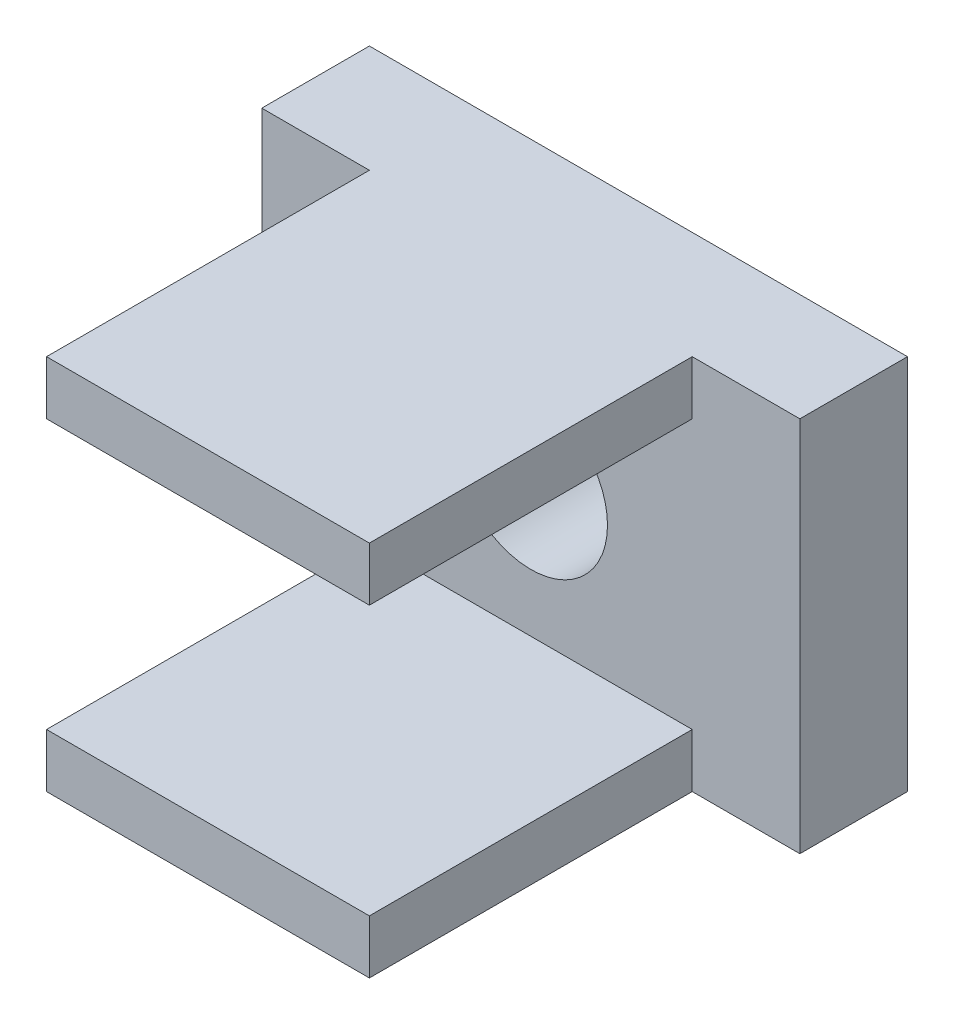
SolidWorks part; units mm, degrees
ref_plane "Front Plane" through (0, 0, 0) normal (0, 0, 1) x (1, 0, 0)
ref_plane "Top Plane" through (0, 0, 0) normal (0, 1, 0) x (1, 0, 0)
ref_plane "Right Plane" through (0, 0, 0) normal (1, 0, 0) x (0, 0, -1)
sketch "Sketch1" plane through (0, 0, 0) normal (0, 0, 1) x (1, 0, 0)
  line L1 (-5, -3.5) -> (5, -3.5)
  line L2 (-5, -3.5) -> (-5, 3.5)
  line L3 (-5, 3.5) -> (5, 3.5)
  line L4 (5, -3.5) -> (5, 3.5)
  line L5 (-5, -3.5) -> (5, 3.5) construction
  line L6 (-5, 3.5) -> (5, -3.5) construction
  point P0 (0, 0)
  dimension "D1" = 10
  dimension "D2" = 7
extrude "Boss-Extrude1" add sketch "Sketch1" along normal blind 2
sketch "Sketch2" plane through (0, 0, 2) normal (0, 0, 1) x (1, 0, 0)
  circle A0 centre (0, 0) radius 1.425
  dimension "D1" = 2.85
extrude "Cut-Extrude1" cut sketch "Sketch2" against normal through all
sketch "Sketch3" plane through (0, 0, 2) normal (0, 0, 1) x (1, 0, 0)
  line L0 (0, 3.5) -> (0, -3.5) construction
  line L1 (5, 3.5) -> (-5, 3.5) construction
  line L2 (-5, -3.5) -> (5, -3.5) construction
  line L4 (-3, 3.5) -> (3, 3.5)
  line L5 (-3, 3.5) -> (-3, 2.5)
  line L6 (-3, 2.5) -> (3, 2.5)
  line L7 (3, 3.5) -> (3, 2.5)
  line L8 (-3, -3.5) -> (3, -3.5)
  line L9 (-3, -3.5) -> (-3, -2.5)
  line L10 (-3, -2.5) -> (3, -2.5)
  line L11 (3, -3.5) -> (3, -2.5)
  dimension "D1" = 1
  dimension "D2" = 6
  dimension "D3" = 1
extrude "Boss-Extrude2" add sketch "Sketch3" along normal blind 6
